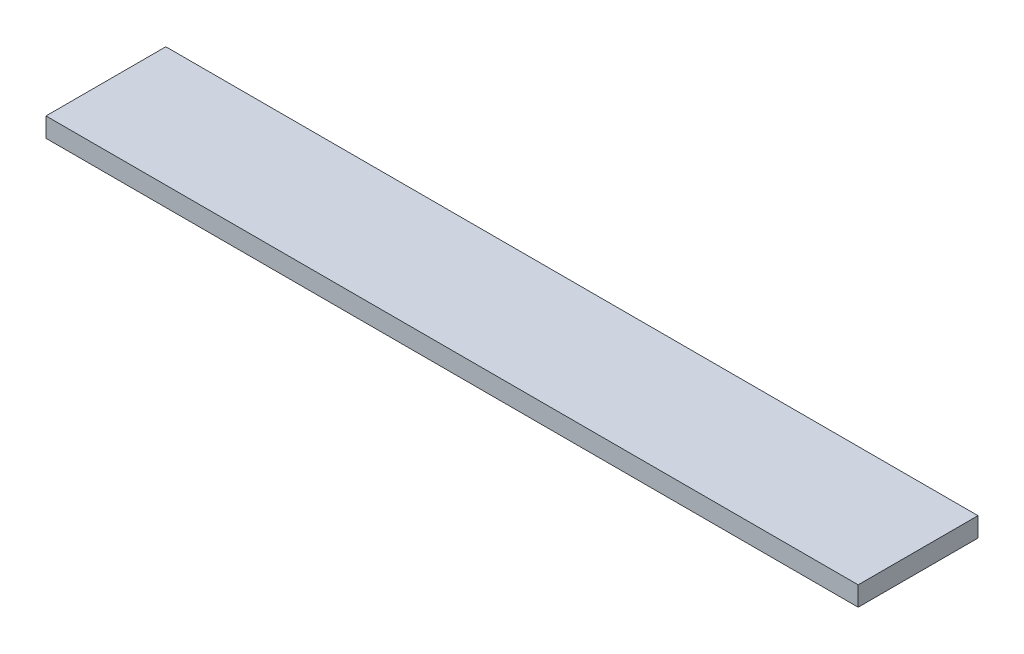
SolidWorks part; units mm, degrees
ref_plane "Front Plane" through (0, 0, 0) normal (0, 0, 1) x (1, 0, 0)
ref_plane "Top Plane" through (0, 0, 0) normal (0, 1, 0) x (1, 0, 0)
ref_plane "Right Plane" through (0, 0, 0) normal (1, 0, 0) x (0, 0, -1)
sketch "Sketch1" plane through (0, 0, 0) normal (0, 1, 0) x (1, 0, 0)
  line L1 (-30.5, 4.5) -> (30.5, 4.5)
  line L2 (-30.5, 4.5) -> (-30.5, -4.5)
  line L3 (-30.5, -4.5) -> (30.5, -4.5)
  line L4 (30.5, 4.5) -> (30.5, -4.5)
  line L5 (-30.5, 4.5) -> (30.5, -4.5) construction
  line L6 (-30.5, -4.5) -> (30.5, 4.5) construction
  point P0 (0, 0)
  dimension "D1" = 9
  dimension "D2" = 61
extrude "Boss-Extrude1" add sketch "Sketch1" along normal blind 1.46
